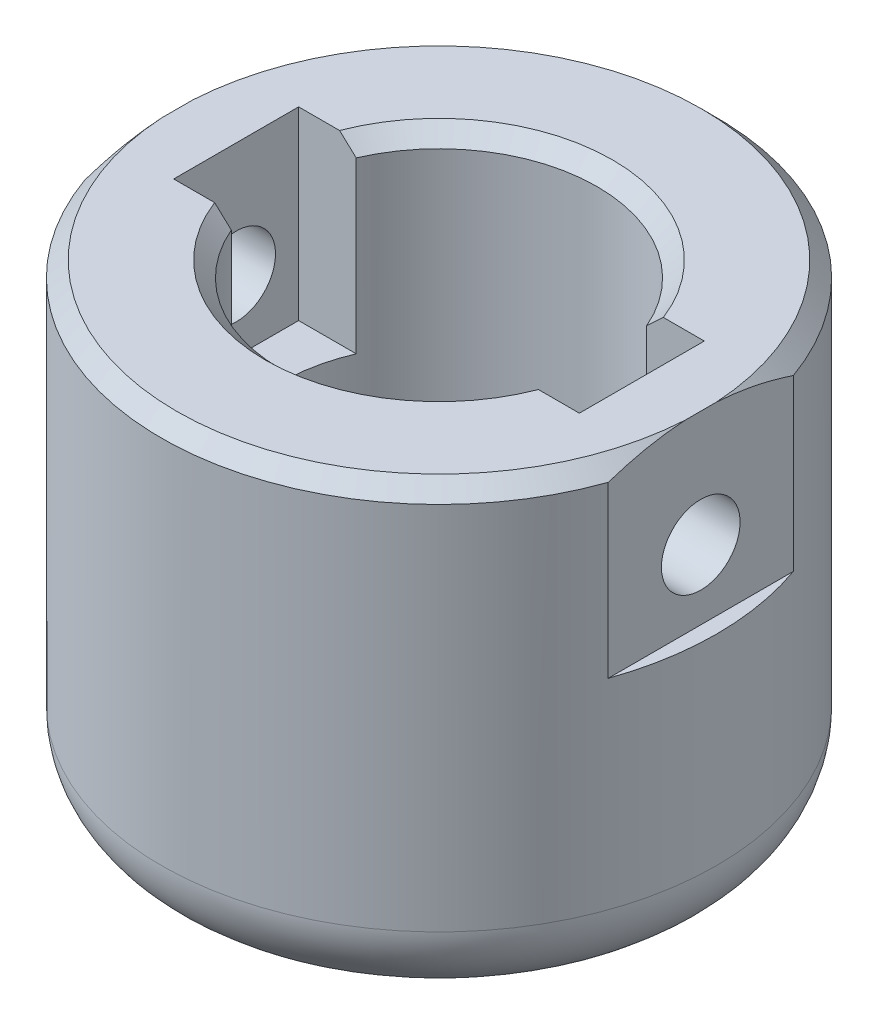
SolidWorks part; units mm, degrees
ref_plane "Front Plane" through (0, 0, 0) normal (0, 0, 1) x (1, 0, 0)
ref_plane "Top Plane" through (0, 0, 0) normal (0, 1, 0) x (1, 0, 0)
ref_plane "Right Plane" through (0, 0, 0) normal (1, 0, 0) x (0, 0, -1)
sketch "Sketch1" plane through (0, 0, 0) normal (0, 0, 1) x (1, 0, 0)
  line L0 (0, -427.0952) -> (0, 20927.6644) construction
  line L1 (-427.0952, 0) -> (20927.6644, 0) construction
  line L2 (18, 0) -> (5.25, 0)
  line L3 (10.25, 0) -> (18, 0) construction
  line L4 (10.25, 0) -> (10.25, 30) construction
  line L5 (10.25, 30) -> (18, 30)
  line L6 (18, 0) -> (18, 30)
  line L7 (5.25, 0) -> (5.25, 3)
  line L8 (5.25, 3) -> (10.25, 3)
  line L9 (10.25, 3) -> (10.25, 30)
  dimension "D1" = 10.25
  dimension "D2" = 36
  dimension "D3" = 30
  dimension "D4" = 3
  dimension "D5" = 10.5
revolve "Revolve1" add sketch "Sketch1" angle 360 about L0
fillet "Fillet1" radius 1 1 edges at (10.25, 3, 0)
chamfer "Chamfer1" distance 1 angle 45 2 edges at (10.25, 30, 0) (18, 30, 0)
fillet "Fillet2" radius 5 1 edges at (18, 0, 0)
sketch "Sketch3" plane through (0, 30, 0) normal (0, 1, 0) x (1, 0, 0)
  line L0 (0, -1000) -> (0, 49000) construction
  line L1 (-1000, 0) -> (49000, 0) construction
  line L2 (-13.15, 4.05) -> (-9.4159, 4.05)
  line L3 (-13.15, -4.05) -> (-10.15, -4.05) construction
  line L4 (-13.15, -4.05) -> (-13.15, 4.05)
  line L5 (-13.15, 4.05) -> (-10.15, 4.05) construction
  line L6 (-10.15, -4.05) -> (-10.15, 4.05) construction
  line L7 (-13.15, -4.05) -> (-10.15, 4.05) construction
  line L8 (-13.15, 4.05) -> (-10.15, -4.05) construction
  line L9 (-13.15, -4.05) -> (-9.4159, -4.05)
  line L10 (13.15, -4.05) -> (13.15, 4.05)
  line L11 (13.15, 4.05) -> (9.4159, 4.05)
  line L12 (13.15, -4.05) -> (9.4159, -4.05)
  line L13 (18.9706, 6) -> (16.9706, 6)
  line L14 (-18.9706, -6) -> (-16.9706, -6)
  line L15 (-18.9706, -6) -> (-18.9706, 6)
  line L16 (-18.9706, 6) -> (-16.9706, 6)
  line L17 (-16.9706, -6) -> (-16.9706, 6)
  line L18 (-18.9706, -6) -> (-16.9706, 6) construction
  line L19 (-18.9706, 6) -> (-16.9706, -6) construction
  line L20 (16.9706, -6) -> (16.9706, 6)
  line L21 (18.9706, -6) -> (16.9706, -6)
  line L22 (18.9706, -6) -> (18.9706, 6)
  circle A3 centre (0, 0) radius 10.25 construction
  arc A4 (9.4159, -4.05) -> (9.4159, 4.05) centre (0, 0) ccw
  arc A5 (-9.4159, 4.05) -> (-9.4159, -4.05) centre (0, 0) ccw
  circle A6 centre (0, 0) radius 18 construction
  point P4 (-11.65, 0)
  point P11 (-10.15, 0)
  point P12 (-10.25, 0)
  point P15 (-17.9706, 0)
  point P26 (-18, 0)
  dimension "D1" = 3
  dimension "D2" = 0.1
  dimension "D3" = 8.1
  dimension "D4" = 12
  dimension "D5" = 2
extrude "Cut-Extrude1" cut sketch "Sketch3" against normal blind 12
sketch "Sketch4" plane through (0, 0, 0) normal (1, 0, 0) x (0, 0, -1)
  line L0 (0, -1000) -> (0, 49000) construction
  line L1 (17, 30) -> (-17, 30) construction
  circle A0 centre (0, 22.5) radius 2.55
  dimension "D1" = 5.1
  dimension "D2" = 7.5
extrude "Cut-Extrude2" cut sketch "Sketch4" against normal through all both and the other way through all
